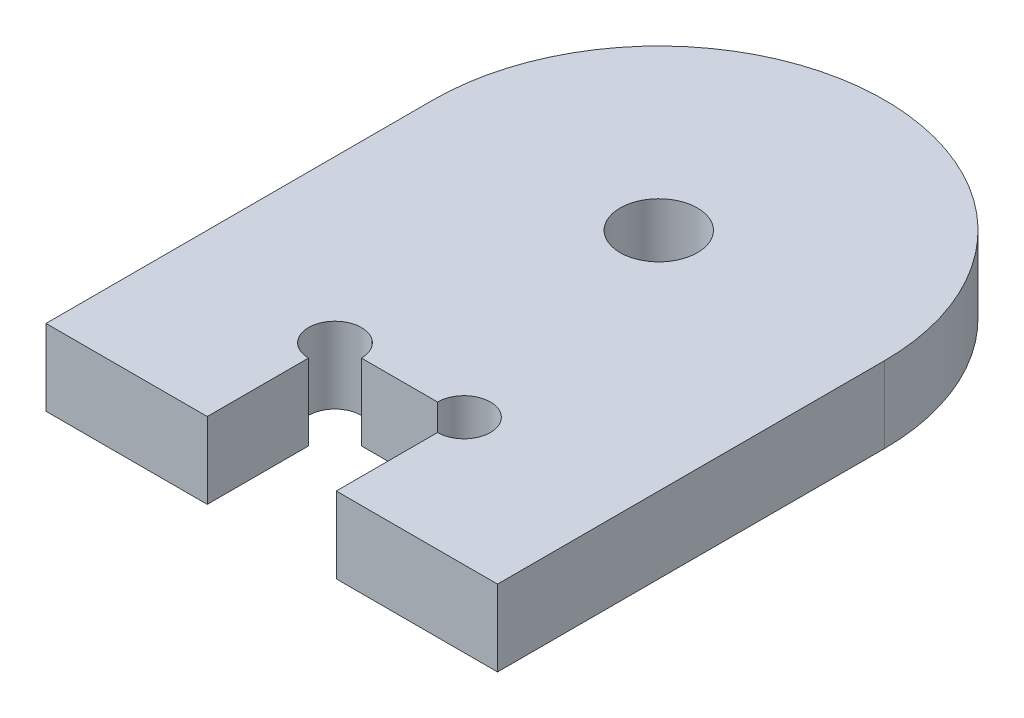
SolidWorks part; units mm, degrees
ref_plane "Front Plane" through (0, 0, 0) normal (0, 0, 1) x (1, 0, 0)
ref_plane "Top Plane" through (0, 0, 0) normal (0, 1, 0) x (1, 0, 0)
ref_plane "Right Plane" through (0, 0, 0) normal (1, 0, 0) x (0, 0, -1)
sketch "Sketch1" plane through (0, 0, 0) normal (0, 1, 0) x (1, 0, 0)
  line L1 (-17.5, 12.5) -> (17.5, 12.5)
  line L2 (-17.5, 12.5) -> (-17.5, -12.5)
  line L3 (-17.5, -12.5) -> (17.5, -12.5)
  line L4 (17.5, 12.5) -> (17.5, -12.5)
  line L5 (-17.5, 12.5) -> (17.5, -12.5) construction
  line L6 (-17.5, -12.5) -> (17.5, 12.5) construction
  circle A0 centre (0, 12.5) radius 17.5
  circle A3 centre (0, 12.5) radius 3
  point P0 (0, 0)
  point P28 (0, 12.5)
  dimension "D6" = 6
  dimension "D1" = 25
  dimension "D2" = 35
extrude "Boss-Extrude1" add sketch "Sketch1" along normal blind 5.9
sketch "Sketch2" plane through (0, 5.9, 0) normal (0, 1, 0) x (1, 0, 0)
  line L1 (-5, -19.4) -> (5, -19.4)
  line L2 (-5, -19.4) -> (-5, -7.6)
  line L3 (-5, -7.6) -> (5, -7.6)
  line L4 (5, -19.4) -> (5, -7.6)
  line L5 (-5, -19.4) -> (5, -7.6) construction
  line L6 (-5, -7.6) -> (5, -19.4) construction
  point P0 (0, -13.5)
  dimension "D1" = 10
  dimension "D2" = 11.8
  dimension "D3" = 13.5
extrude "Cut-Extrude1" cut sketch "Sketch2" against normal up to next
sketch "Sketch3" plane through (0, 0, 12.5) normal (0, 0, 1) x (1, 0, 0)
  line L4 (-17.5, 0) -> (-5, 0)
  line L5 (-5, 0) -> (-5, 5.9)
  line L6 (-5, 5.9) -> (-17.5, 5.9)
  line L7 (-17.5, 5.9) -> (-17.5, 0)
  line L8 (-17.5, 0) -> (-5, 0)
  line L9 (-5, 0) -> (-5, 5.9)
  line L10 (-5, 5.9) -> (-17.5, 5.9)
  line L11 (-17.5, 5.9) -> (-17.5, 0)
  line L12 (17.5, 5.9) -> (5, 5.9)
  line L13 (5, 5.9) -> (5, 0)
  line L14 (5, 0) -> (17.5, 0)
  line L15 (17.5, 0) -> (17.5, 5.9)
  line L16 (17.5, 5.9) -> (5, 5.9)
  line L17 (5, 5.9) -> (5, 0)
  line L18 (5, 0) -> (17.5, 0)
  line L19 (17.5, 0) -> (17.5, 5.9)
  dimension "D1" = 0
  dimension "D2" = 0
extrude "Boss-Extrude2" add sketch "Sketch3" along normal blind 5
sketch "Sketch4" plane through (0, 5.9, 0) normal (0, 1, 0) x (1, 0, 0)
  circle A0 centre (-5, -7.6) radius 2.05
  circle A1 centre (5, -7.6) radius 2.05
  dimension "D1" = 4.1
extrude "Cut-Extrude2" cut sketch "Sketch4" against normal up to next
equation "\"e\" = 5.9"
equation "\"D1@Boss-Extrude1\"=\"e\""
equation "\"D2@Sketch2\"= 2 * \"e\""
